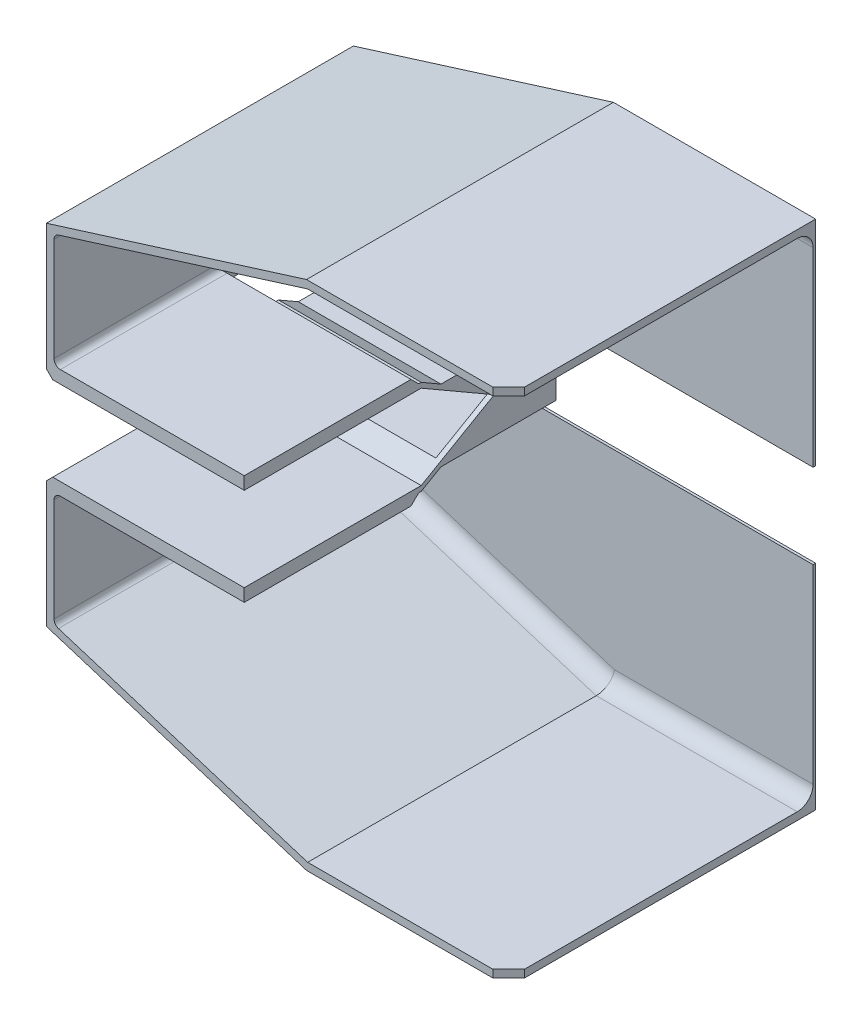
SolidWorks part; units mm, degrees
ref_plane "Front Plane" through (0, 0, 0) normal (0, 0, 1) x (1, 0, 0)
ref_plane "Top Plane" through (0, 0, 0) normal (0, 1, 0) x (1, 0, 0)
ref_plane "Right Plane" through (0, 0, 0) normal (1, 0, 0) x (0, 0, -1)
sketch "Sketch1" plane through (0, 0, 0) normal (0, 0, 1) x (1, 0, 0)
  line L0 (0, 0) -> (145.8, 0) construction
  line L1 (145.8, 0) -> (145.8, 65.8)
  line L2 (145.8, 65.8) -> (82.0337, 65.8)
  line L3 (82.0337, 65.8) -> (0, 40.1645)
  line L4 (0, 40.1645) -> (0, 0)
  line L5 (2.4, 38.4) -> (2.4, 2.4)
  line L6 (2.4, 2.4) -> (143.4, 2.4)
  line L7 (143.4, 2.4) -> (143.4, 63.4)
  line L8 (143.4, 63.4) -> (82.4, 63.4)
  line L9 (82.4, 63.4) -> (2.4, 38.4)
  line L10 (0, 0) -> (0, -1.6)
  line L11 (0, -1.6) -> (145.8, -1.6)
  line L12 (145.8, -1.6) -> (145.8, 0)
  dimension "D2" = 141
  dimension "D3" = 61
  dimension "D4" = 36
  dimension "D5" = 80
  dimension "D6" = 4
  dimension "D1" = 2.4
extrude "Boss-Extrude1" add sketch "Sketch1" along normal blind 96
sketch "Sketch2" plane through (0, 0, 0) normal (0, 0, -1) x (-1, 0, 0)
  line L0 (-145.8, 0) -> (-145.8, 65.8) construction
  line L1 (-145.8, 65.8) -> (-82.0337, 65.8) construction
  line L3 (0, 40.1645) -> (0, 0) construction
  line L4 (-82.0337, 65.8) -> (0, 40.1645) construction
  line L5 (-145.8, 0) -> (-145.8, 65.8)
  line L6 (-145.8, 65.8) -> (-82.0337, 65.8)
  line L8 (0, 40.1645) -> (0, 0)
  line L9 (-82.0337, 65.8) -> (0, 40.1645)
  line L11 (0, 0) -> (0, -1.6) construction
  line L12 (0, -1.6) -> (-145.8, -1.6) construction
  line L13 (-145.8, -1.6) -> (-145.8, 0) construction
  line L14 (0, 0) -> (0, -1.6)
  line L15 (0, -1.6) -> (-145.8, -1.6)
  line L16 (-145.8, -1.6) -> (-145.8, 0)
extrude "Boss-Extrude2" add sketch "Sketch2" along normal blind 2.4
sketch "Sketch3" plane through (0, 0, 96) normal (0, 0, 1) x (1, 0, 0)
  line L0 (145.8, 0) -> (145.8, 65.8) construction
  line L1 (143.4, 63.4) -> (145.8, 63.4)
  line L2 (143.4, 63.4) -> (143.4, 2.4)
  line L3 (143.4, 2.4) -> (145.8, 2.4)
  line L4 (145.8, 63.4) -> (145.8, 2.4)
  line L5 (144.6, 2.4) -> (144.6, 63.4) construction
  line L6 (143.4, 32.9) -> (145.8, 32.9) construction
  line L7 (143.4, 2.4) -> (143.4, 63.4) construction
  point P224 (144.6, 32.9)
extrude "Cut-Extrude1" cut sketch "Sketch3" against normal up to surface (96 mm away) up to face at (74.8, 34, 0)
sketch "Sketch4" plane through (0, 2.4, 0) normal (0, 1, 0) x (1, 0, 0)
  line L0 (2.4, 0) -> (143.4, 0) construction
  line L1 (2.4, 0) -> (145.8, 0)
  line L2 (2.4, 0) -> (2.4, -41)
  line L3 (2.4, -41) -> (145.8, -41)
  line L4 (145.8, 0) -> (145.8, -41)
  line L5 (74.1, -41) -> (74.1, 0) construction
  line L6 (2.4, -20.5) -> (145.8, -20.5) construction
  line L7 (0, 0) -> (145.8, 0) construction
  point P1008 (74.1, -20.5)
  dimension "D1" = 41
extrude "Cut-Extrude2" cut sketch "Sketch4" against normal through all
sketch "Sketch9" plane through (0, 2.4, 0) normal (0, 1, 0) x (1, 0, 0)
  line L0 (2.4, -96) -> (145.8, -96) construction
  line L1 (145.8, -41) -> (62.4, -41)
  line L2 (145.8, -41) -> (145.8, -96)
  line L3 (145.8, -96) -> (62.4, -96)
  line L4 (62.4, -41) -> (62.4, -96)
  line L5 (104.1, -96) -> (104.1, -41) construction
  line L6 (145.8, -68.5) -> (62.4, -68.5) construction
  line L7 (2.4, -96) -> (2.4, -41) construction
  point P300 (104.1, -68.5)
  dimension "D1" = 60
extrude "Cut-Extrude4" cut sketch "Sketch9" against normal through all
sketch "Sketch5" plane through (62.4, 0, 0) normal (1, 0, 0) x (0, 0, -1)
  line L0 (-41, 0) -> (-43.4, 2.4)
  line L1 (-41, -1.6) -> (-41, 2.4) construction
  line L2 (-41, 2.4) -> (-96, 2.4) construction
  line L3 (-43.4, 2.4) -> (-41, 2.4)
  line L4 (-41, 2.4) -> (-41, 0)
  line L5 (-41, -1.6) -> (-41, 2.4) construction
  dimension "D1" = 1.6
extrude "Cut-Extrude3" cut sketch "Sketch5" against normal up to surface (60 mm away) up to face at (2.4, 13.0667, 45.6667)
sketch "Sketch6" plane through (62.4, 0, 0) normal (1, 0, 0) x (0, 0, -1)
  line L0 (-40.2, 0) -> (-41, 0)
  line L1 (-41, 0) -> (-41, -1.6)
  line L2 (-41, -1.6) -> (-40.2, -1.6)
  line L3 (-40.2, -1.6) -> (-33.9646, -5.2)
  line L4 (-33.9646, -5.2) -> (2.4, -5.2)
  line L5 (2.4, -5.2) -> (2.4, -3.6)
  line L6 (2.4, -3.6) -> (-33.9646, -3.6)
  line L7 (-33.9646, -3.6) -> (-40.2, 0)
  line L8 (0, -1.6) -> (-41, -1.6) construction
  line L9 (2.4, 65.8) -> (2.4, -1.6) construction
  line L10 (-40.2, -1.6) -> (-40.2, 0) construction
  dimension "D1" = 30
  dimension "D2" = 2
  dimension "D3" = 0.8
  dimension "D4" = 1.6
extrude "Boss-Extrude3" add sketch "Sketch6" against normal offset from surface (45 mm away) 15 up to face at (2.4, 11.2, 45.3429)
ref_plane "Plane1" through (39.9, 0, 0) normal (1, 0, 0) x (0, 0, -1)
sketch "Sketch8" plane through (62.4, 0, 0) normal (1, 0, 0) x (0, 0, -1)
  line L0 (-33.9646, -5.2) -> (2.4, -26.1951)
  line L1 (2.4, -26.1951) -> (2.4, -5.2)
  line L2 (-33.9646, -5.2) -> (2.4, -5.2)
  line L3 (-40.2, -1.6) -> (-33.9646, -5.2) construction
extrude "Boss-Extrude4" add sketch "Sketch8" against normal blind 1.6
mirror "Mirror1" about plane through (39.9, 0, 0) normal (1, 0, 0) of "Boss-Extrude4"
chamfer "Chamfer1" distance 5 angle 45 1 edges at (145.8, 64.6, 96)
fillet "Fillet1" radius 2 1 edges at (2.4, 2.4, 69.7)
fillet "Fillet3" radius 5 3 edges at (114.1, 63.4, 0) (42.4, 50.9, 0) (2.4, 18.4, 0)
fillet "Fillet4" radius 2 2 edges at (3.8645, 37.3233, 1.4645) (2.4, 38.4, 50.5)
chamfer "Chamfer2" distance 1.6 angle 45 5 edges at (113.9169, 65.8, -2.4) (41.0169, 52.9822, -2.4) (0, 19.2822, -2.4) (72.9, -1.6, -2.4) (145.8, 32.1, -2.4)
chamfer "Chamfer3" distance 2 angle 45 1 edges at (0, -1.6, 47.6)
ref_plane "Plane2" through (0, -14.8976, 0) normal (0, 1, 0) x (1, 0, 0)
mirror "Mirror2" about plane through (0, -14.8976, 0) normal (0, 1, 0) of bodies 108
